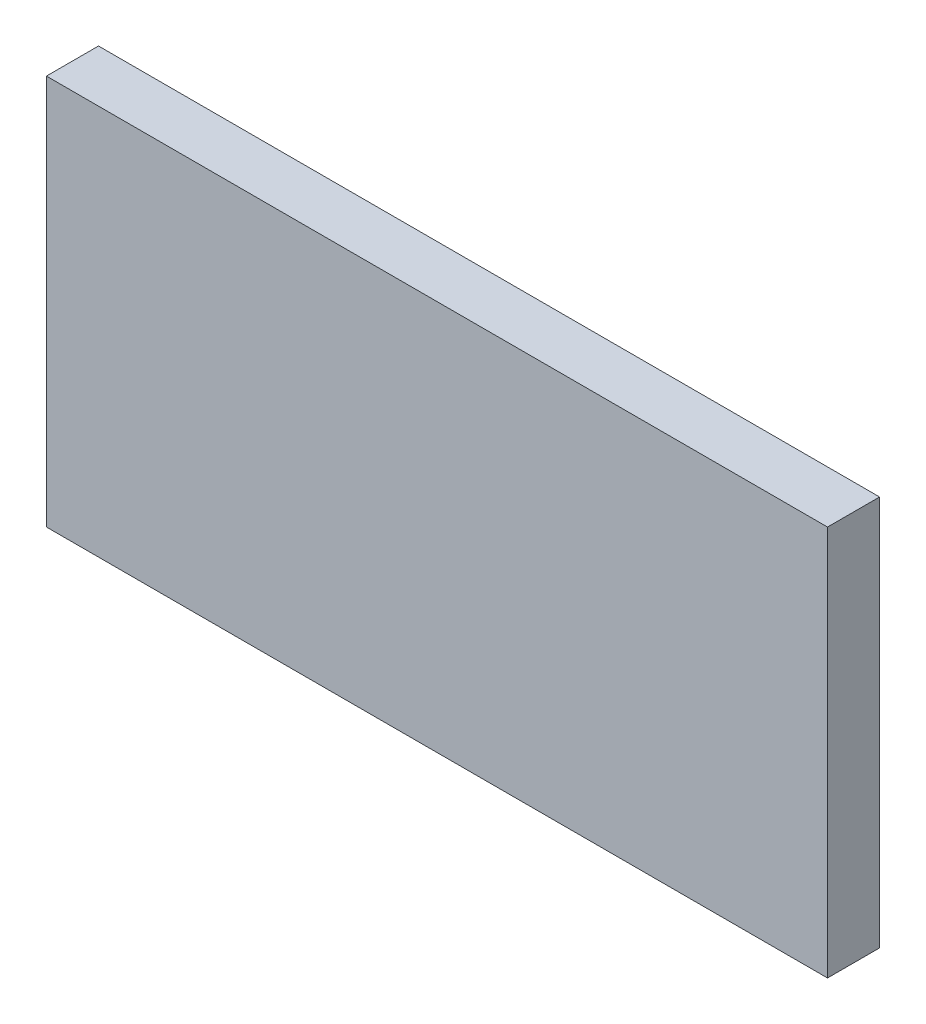
SolidWorks part; units mm, degrees
ref_plane "Front Plane" through (0, 0, 0) normal (0, 0, 1) x (1, 0, 0)
ref_plane "Top Plane" through (0, 0, 0) normal (0, 1, 0) x (1, 0, 0)
ref_plane "Right Plane" through (0, 0, 0) normal (1, 0, 0) x (0, 0, -1)
sketch "Sketch1" plane through (0, 0, 0) normal (0, 0, 1) x (1, 0, 0)
  line L1 (150, -75) -> (-150, -75)
  line L2 (150, -75) -> (150, 75)
  line L3 (150, 75) -> (-150, 75)
  line L4 (-150, -75) -> (-150, 75)
  line L5 (150, -75) -> (-150, 75) construction
  line L6 (150, 75) -> (-150, -75) construction
  point P0 (0, 0)
  dimension "D1" = 300
  dimension "D2" = 150
extrude "Boss-Extrude1" add sketch "Sketch1" along normal blind 20
sketch "Sketch2" plane through (0, 0, 0) normal (0, 0, -1) x (-1, 0, 0)
  line L1 (90.25, -15) -> (10, -15)
  line L2 (90.25, -15) -> (90.25, 15)
  line L3 (90.25, 15) -> (10, 15)
  line L4 (10, -15) -> (10, 15)
  line L5 (-150, 75) -> (150, 75) construction
  line L6 (-150, -75) -> (-150, 75) construction
  point P0 (0, 0)
  dimension "D1" = 80.25
  dimension "D2" = 30
  dimension "D3" = 60
  dimension "160" = 160
extrude "Cut-Extrude1" cut sketch "Sketch2" against normal blind 15
ref_plane "Plane1" through (0, 30, 0) normal (0, 1, 0) x (1, 0, 0)
sketch "Sketch3" plane through (0, 30, 0) normal (0, 1, 0) x (1, 0, 0)
  line L0 (56.38, 0) -> (56.38, 12.86)
  line L1 (150, 0) -> (-150, 0) construction
  line L2 (96.38, 12.86) -> (96.38, 0)
  line L3 (96.38, 0) -> (56.38, 0)
  arc A0 (56.38, 12.86) -> (96.38, 12.86) centre (76.38, 12.86) cw
  circle A1 centre (76.38, 12.86) radius 10
  dimension "D3" = 20
  dimension "D4" = 20
  dimension "D1" = 73.62
  dimension "D2" = 12.86
extrude "Boss-Extrude2" add sketch "Sketch3" against normal blind 20
